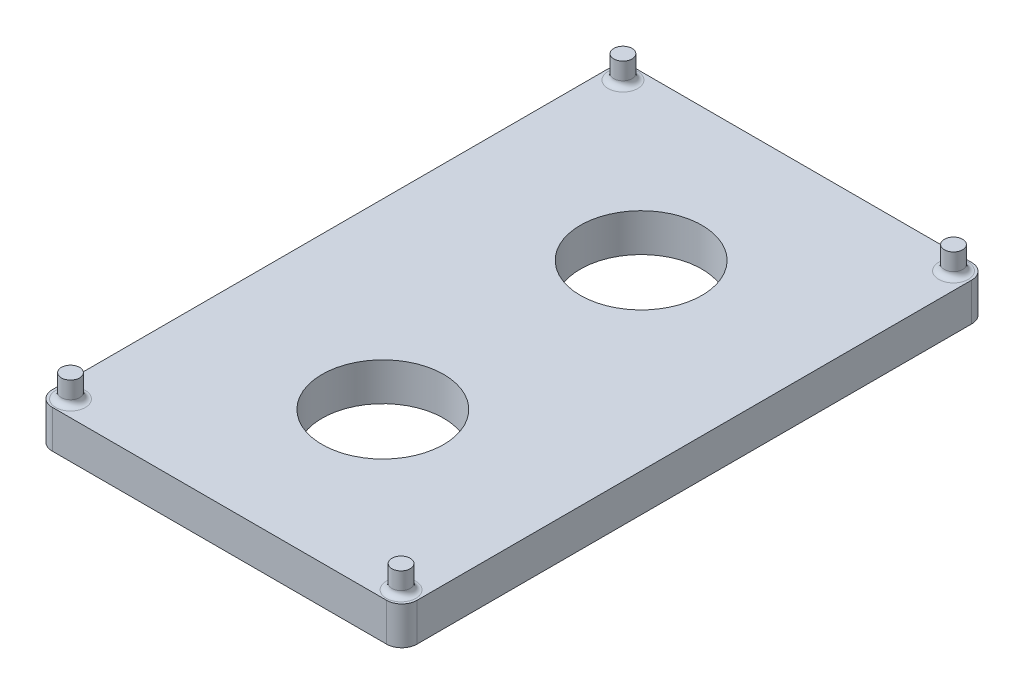
SolidWorks part; units mm, degrees
ref_plane "Front Plane" through (0, 0, 0) normal (0, 0, 1) x (1, 0, 0)
ref_plane "Top Plane" through (0, 0, 0) normal (0, 1, 0) x (1, 0, 0)
ref_plane "Right Plane" through (0, 0, 0) normal (1, 0, 0) x (0, 0, -1)
sketch "Sketch1" plane through (0, 0, 0) normal (0, 1, 0) x (1, 0, 0)
  line L0 (-19.8396, 39.6995) -> (-22.0896, 39.6995) construction
  line L1 (-22.0896, 41.8495) -> (25.9104, 41.8495)
  line L2 (-22.0896, 41.8495) -> (-22.0896, -35.1505)
  line L3 (-22.0896, -35.1505) -> (25.9104, -35.1505)
  line L4 (25.9104, 41.8495) -> (25.9104, -35.1505)
  line L5 (23.6604, 39.6995) -> (25.9104, 39.6995) construction
  line L6 (-19.8396, 39.6995) -> (-19.8396, 41.8495) construction
  line L7 (-19.8396, -33.0005) -> (-19.8396, -35.1505) construction
  dimension "D1" = 48
  dimension "D2" = 77
extrude "Boss-Extrude1" add sketch "Sketch1" along normal blind 5
sketch "Sketch2" plane through (0, 5, 0) normal (0, 1, 0) x (1, 0, 0)
  line L0 (-19.8396, 39.6995) -> (-19.8396, 41.8495) construction
  line L1 (25.9104, 41.8495) -> (-22.0896, 41.8495) construction
  line L2 (-19.8396, 41.8495) -> (-22.0896, 41.8495) construction
  line L3 (-22.0896, 41.8495) -> (-22.0896, 39.6995) construction
  line L4 (-22.0896, 41.8495) -> (-22.0896, -35.1505) construction
  line L5 (-22.0896, 39.6995) -> (-19.8396, 39.6995) construction
  line L6 (23.6604, 39.6995) -> (25.9104, 39.6995) construction
  line L7 (25.9104, -35.1505) -> (25.9104, 41.8495) construction
  line L8 (-19.8396, -33.0005) -> (-19.8396, -35.1505) construction
  line L9 (-22.0896, -35.1505) -> (25.9104, -35.1505) construction
  circle A0 centre (-19.8396, 39.6995) radius 1.2
  circle A1 centre (23.6604, 39.6995) radius 1.2
  circle A2 centre (23.6604, -33.0005) radius 1.2
  circle A3 centre (-19.8396, -33.0005) radius 1.2
  dimension "D1" = 2.4
  dimension "D2" = 2
  dimension "D3" = 2
extrude "Boss-Extrude2" add sketch "Sketch2" along normal blind 3
fillet "Fillet1" radius 0.75 4 edges at (-19.8396, 5, 34.2005) (23.6604, 5, 34.2005) (23.6604, 5, -38.4995) (-19.8396, 5, -38.4995)
fillet "Fillet2" radius 2 4 edges at (-22.0896, 2.5, 35.1505) (25.9104, 2.5, 35.1505) (25.9104, 2.5, -41.8495) (-22.0896, 2.5, -41.8495)
sketch "Sketch3" plane through (0, 5, 0) normal (0, 1, 0) x (1, 0, 0)
  line L0 (1.9104, 41.8495) -> (1.9104, -35.1505) construction
  line L1 (23.9104, 41.8495) -> (-20.0896, 41.8495) construction
  line L2 (-20.0896, -35.1505) -> (23.9104, -35.1505) construction
  line L3 (-22.0896, 3.3495) -> (25.9104, 3.3495) construction
  line L4 (-22.0896, 39.8495) -> (-22.0896, -33.1505) construction
  line L5 (25.9104, -33.1505) -> (25.9104, 39.8495) construction
  circle A0 centre (1.9104, 20.3442) radius 8
  circle A1 centre (1.9104, -13.6452) radius 8
  dimension "D1" = 16
extrude "Cut-Extrude1" cut sketch "Sketch3" against normal through all
